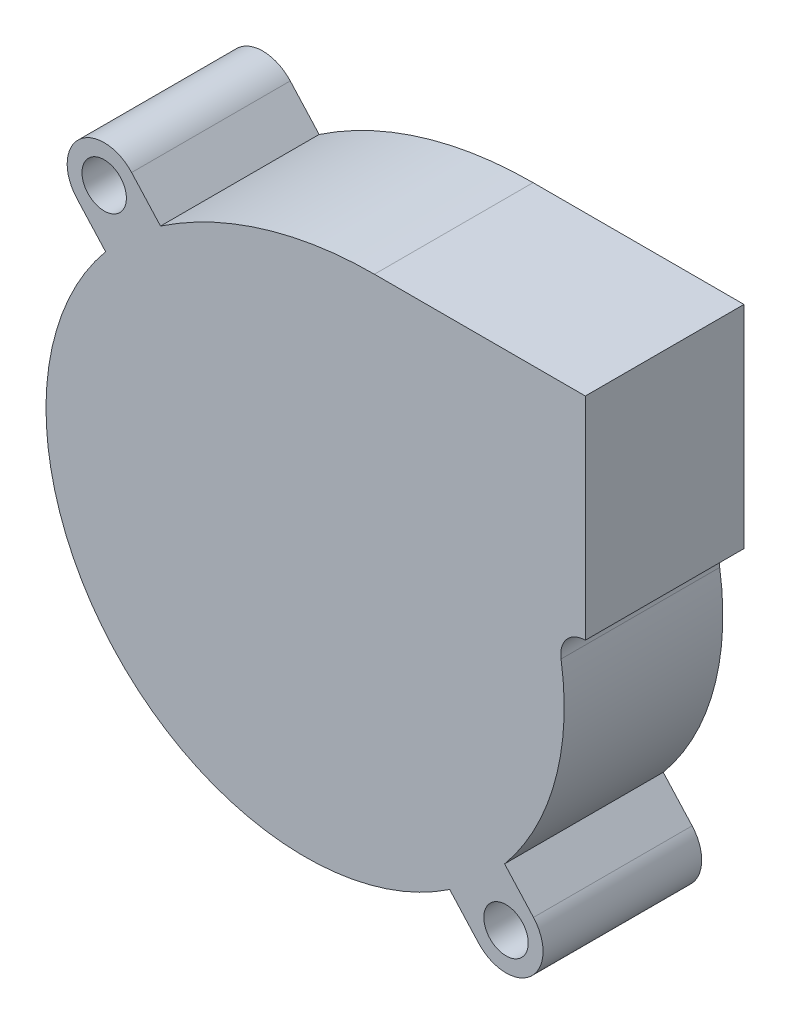
SolidWorks part; units mm, degrees
material "6061-T6 Black anodised"
ref_plane "Front Plane" through (0, 0, 0) normal (0, 0, 1) x (1, 0, 0)
ref_plane "Top Plane" through (0, 0, 0) normal (0, 1, 0) x (1, 0, 0)
ref_plane "Right Plane" through (0, 0, 0) normal (1, 0, 0) x (0, 0, -1)
sketch "Sketch1" plane through (0, 0, 0) normal (0, 0, 1) x (1, 0, 0)
  line L0 (-19, 21) -> (19, -21) construction
  line L1 (-24.5, 0) -> (24.5, 0) construction
  line L2 (-21.5954, 18.6518) -> (-18.8642, 15.6331)
  line L3 (21.5954, -18.6518) -> (18.8642, -15.6331)
  line L4 (-13.6734, 20.3295) -> (-16.4046, 23.3482)
  line L5 (13.6734, -20.3295) -> (16.4046, -23.3482)
  line L7 (26.5, 26.5) -> (6.5572, 26.5)
  line L8 (26.5, 26.5) -> (26.5, 6.5)
  arc A0 (-18.8642, 15.6331) -> (13.6734, -20.3295) centre (0, 0) ccw
  circle A1 centre (-19, 21) radius 2.1
  circle A2 centre (19, -21) radius 2.1
  arc A3 (-16.4046, 23.3482) -> (-21.5954, 18.6518) centre (-19, 21) ccw
  arc A4 (16.4046, -23.3482) -> (21.5954, -18.6518) centre (19, -21) ccw
  arc A5 (18.8642, -15.6331) -> (24.2017, 3.8114) centre (0, 0) ccw
  arc A6 (26.5, 6.5) -> (24.2017, 3.8114) centre (26.5, 4.1734) ccw
  arc A7 (6.5572, 26.5) -> (-13.6734, 20.3295) centre (6.5572, -9.7491) ccw
  arc A8 (24.2017, 3.8114) -> (-13.6734, 20.3295) centre (0, 0) ccw construction
  point P20 (0, -24.5)
  dimension "D1" = 49
  dimension "D3" = 4.2
  dimension "D5" = 7.5
  dimension "D2" = 47.5
  dimension "D6" = 51
  dimension "D7" = 51
  dimension "D8" = 20
extrude "Boss-Extrude1" add sketch "Sketch1" along normal blind 15
